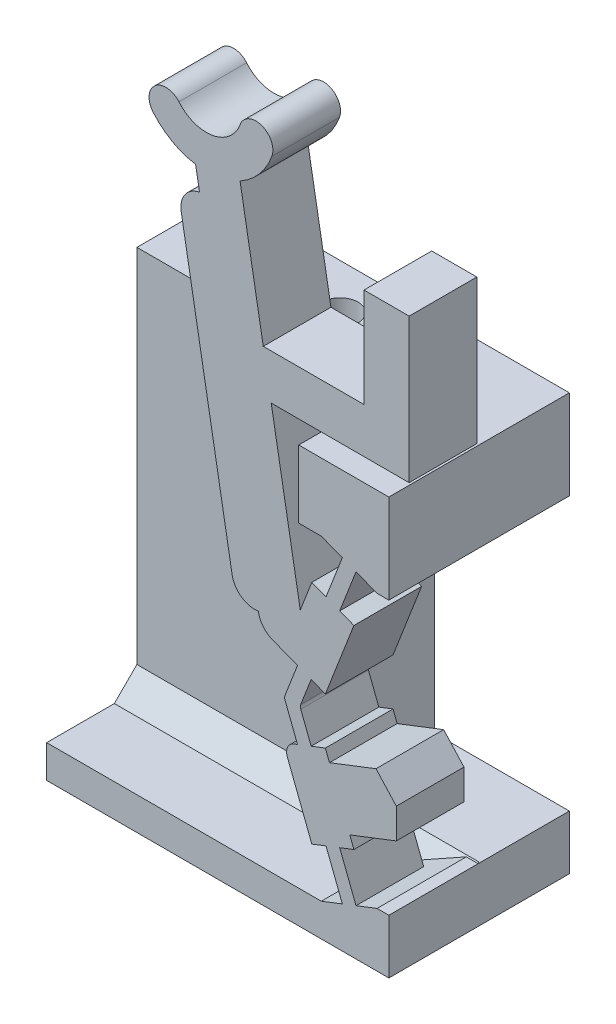
SolidWorks part; units mm, degrees
material "Nylon 6/12"
ref_plane "Front Plane" through (0, 0, 0) normal (0, 0, 1) x (1, 0, 0)
ref_plane "Top Plane" through (0, 0, 0) normal (0, 1, 0) x (1, 0, 0)
ref_plane "Right Plane" through (0, 0, 0) normal (1, 0, 0) x (0, 0, -1)
sketch "Sketch-SkeletonConfigUp" plane through (0, 0, 0) normal (0, 0, 1) x (1, 0, 0)
  line L0 (0, 0) -> (0, -50000) construction
  line L1 (-1.4217, 8.457) -> (-1.4217, 0) construction
  line L3 (0.7468, 14.0514) -> (-1.4217, 8.457) construction
  line L4 (-1.4217, 8.457) -> (0.7468, 2.8626) construction
  line L5 (0.7468, 14.0514) -> (2.1074, 19.3343) construction
  line L6 (-1.4217, 8.457) -> (-5.2203, 30) construction
  line L9 (0.7468, 14.0514) -> (0.7468, 2.8626) construction
  line L10 (0.7468, 2.8626) -> (0.7468, 0) construction
  line L11 (0, 0) -> (0.7468, 0) construction
  line L12 (0.7468, 0) -> (0, 0) construction
  dimension "D7" = 5.4552
  dimension "D10" = 6.745
  dimension "D3" = 2.1685
  dimension "D9" = 10
  dimension "D13" = 11.1888
  dimension "D14" = 30
  dimension "D5" = 10
  dimension "D2" = 21.8753
  dimension "D4" = 6
sketch "Sketch-SkeletonConfigDown" plane through (0, 0, 0) normal (0, 0, 1) x (1, 0, 0)
  line L0 (0, 0) -> (0, -50000) construction
  line L1 (0.7468, 14.0514) -> (0.7468, 2.8626) construction
  line L2 (5.9945, 14.5439) -> (0.7468, 14.0514) construction
  line L3 (0.7468, 14.0514) -> (2.9153, 8.457) construction
  line L4 (2.9153, 8.457) -> (0.7468, 2.8626) construction
  line L5 (0.7468, 14.0514) -> (-1.8086, 18.8711) construction
  line L6 (2.9153, 8.457) -> (-13.9344, 22.4075) construction
  line L7 (0.7468, 2.8626) -> (5.9945, 14.5439) construction
  line L8 (-387.6937, -861.8102) -> (5.9945, 14.5439) construction
  line L10 (-1.4217, 8.457) -> (0.7468, 2.8626) construction
  line L11 (0.7468, 14.0514) -> (-1.4217, 8.457) construction
  line L12 (-1.4217, 8.457) -> (-5.2203, 30) construction
  line L13 (0.7468, 14.0514) -> (2.1074, 19.3343) construction
  dimension "D10" = 6.745
  dimension "D4" = 5.2707
  dimension "D5" = 119.553
  dimension "D2" = 50.378
  dimension "D3" = 29.19
ref_plane "Plane-Cam Base" through (3.8672, 0, 0) normal (1, 0, 0) x (0, 0, -1)
ref_plane "Plane-Down-to-Up Derailleur Clearance" through (1.3672, 0, 0) normal (1, 0, 0) x (0, 0, -1)
ref_plane "Plane-Cam Cavity Roof" through (-0.1328, 0, 0) normal (1, 0, 0) x (0, 0, -1)
sketch "Sketch-SwitchBossUp" plane through (0, 0, 0) normal (0, 0, 1) x (1, 0, 0)
  line L8 (-5.6979, 26.9497) -> (-5.5242, 25.9649)
  line L9 (-1.4217, 8.457) -> (-5.2203, 30) construction
  line L15 (-1.1826, 6.941) -> (-0.5766, 7.1759) construction
  line L16 (-1.4217, 8.457) -> (0.7468, 2.8626) construction
  line L19 (0.0824, 13.2365) -> (0.6884, 13.0016) construction
  line L22 (0.8052, 15.1013) -> (1.4113, 14.8664) construction
  line L23 (-1.1826, 9.9731) -> (-1.812, 10.2171)
  line L32 (1.0498, 2.9801) -> (0.4438, 2.7452) construction
  line L40 (-1.7703, 8.457) -> (-1.0732, 8.457) construction
  line L66 (-5.2203, 27.8193) -> (-5.2203, 50027.8193) construction
  line L74 (-4.078, 12.0039) -> (-6.3354, 24.8064)
  line L81 (2.3437, 2.4091) -> (2.8672, 2.4091)
  line L82 (-5.6111, 26.4573) -> (-3.6415, 26.8046) construction
  line L88 (-0.1116, 18.4627) -> (2.8672, 18.4627)
  line L92 (0.6853, 5.7881) -> (-1.1795, 5.0653) construction
  line L95 (-2.3469, 19.4627) -> (3.7672, 19.4627)
  line L96 (2.8672, 14.505) -> (2.8672, 18.4627)
  line L97 (3.7672, 19.4627) -> (3.7672, 25.8576)
  line L101 (-0.8796, 7.0584) -> (-1.4217, 8.457) construction
  line L103 (-5.2203, 30) -> (-3.0238, 29.2005) construction
  line L107 (-1.1826, 9.9731) -> (-0.5766, 9.7382) construction
  line L109 (-5.2203, 30) -> (-7.011, 28.4975) construction
  line L114 (0.0528, 7.4199) -> (-0.5766, 7.1759)
  line L117 (2.8672, 0) -> (-0.1272, 0)
  line L121 (0.7468, 0) -> (0, 0) construction
  line L122 (0.8052, 1.8128) -> (-0.1272, 1.4513)
  line L123 (1.4113, 2.0477) -> (2.3437, 2.4091)
  line L125 (2.8672, 2.4091) -> (2.8672, 0)
  line L127 (-0.5766, 9.7382) -> (0.0528, 9.4942)
  line L133 (0.4438, 14.1689) -> (1.0498, 13.934) construction
  line L134 (0.0528, 9.4942) -> (1.3178, 12.7576)
  line L135 (0.6884, 13.0016) -> (1.3178, 12.7576)
  line L142 (-0.1272, 1.4513) -> (-0.1272, 0)
  line L151 (0.0824, 13.2365) -> (-0.547, 13.4805)
  line L152 (0.8052, 15.1013) -> (0.0824, 13.2365)
  line L153 (1.4113, 14.8664) -> (0.6884, 13.0016)
  line L169 (0.0824, 3.6776) -> (0.8052, 1.8128)
  line L170 (1.4113, 2.0477) -> (0.6884, 3.9125)
  line L177 (0.6884, 3.9125) -> (0.0824, 3.6776) construction
  line L184 (-0.547, 13.4805) -> (-1.0591, 12.1594)
  line L191 (-1.1826, 6.941) -> (-1.812, 6.697)
  line L197 (3.7672, 25.8576) -> (1.7672, 25.8576)
  line L205 (1.7672, 25.8576) -> (1.7672, 21.4627)
  line L207 (12.0045, 16.6962) -> (12.0045, 16.6883) construction
  line L218 (0.6884, 3.9125) -> (1.3178, 4.1564)
  line L225 (-1.0591, 12.1594) -> (-2.3469, 19.4627)
  line L235 (-5.5242, 25.9649) -> (-2.8161, 10.6063) construction
  line L236 (-1.812, 6.697) -> (-0.547, 3.4336)
  line L237 (-2.8161, 10.6063) -> (-2.9195, 11.1927)
  line L241 (-1.4217, 8.457) -> (-0.8796, 9.8556) construction
  line L242 (1.7672, 21.4627) -> (-2.6996, 21.4627)
  line L243 (-0.5766, 7.1759) -> (-1.0381, 8.3667)
  line L244 (-1.0381, 8.5474) -> (-0.5766, 9.7382)
  line L245 (-1.1826, 6.941) -> (-1.7353, 8.3667)
  line L246 (-1.7353, 8.5474) -> (-1.1826, 9.9731)
  line L247 (0.0528, 7.4199) -> (0.2353, 6.9492)
  line L248 (0.8052, 1.8128) -> (1.4113, 2.0477) construction
  line L249 (0.0824, 3.6776) -> (-0.547, 3.4336)
  line L250 (-1.812, 10.2171) -> (-0.547, 13.4805) construction
  line L251 (0.7468, 14.0514) -> (-1.4217, 8.457) construction
  line L252 (-1.2699, 11.6157) -> (0.5949, 10.8928) construction
  line L253 (-2.3469, 19.4627) -> (-2.6996, 21.4627) construction
  line L254 (-1.812, 10.2171) -> (-2.8161, 10.6063)
  line L255 (0.8052, 15.1013) -> (-0.1272, 15.4627)
  line L256 (1.4113, 14.8664) -> (2.3437, 14.505)
  line L257 (2.3437, 14.505) -> (2.8672, 14.505)
  line L258 (-2.6996, 21.4627) -> (-3.7283, 27.297)
  line L259 (3.8672, -23.7286) -> (3.8672, 23.7286) construction
  line L260 (0.2353, 6.9492) -> (2.2973, 7.7484)
  line L261 (3.1975, 6.7619) -> (3.1975, 5.4265)
  line L262 (3.1975, 5.4265) -> (1.1353, 4.6271)
  line L263 (0.6853, 5.7881) -> (3.1975, 6.7619) construction
  line L264 (1.1353, 4.6271) -> (0.6853, 5.7881) construction
  line L265 (1.1353, 4.6271) -> (1.3178, 4.1564)
  line L266 (0.6853, 5.7881) -> (0.2353, 6.9492) construction
  line L267 (0.2353, 6.9492) -> (0.6853, 5.7881) construction
  line L268 (0.6853, 5.7881) -> (1.1353, 4.6271) construction
  line L269 (0.2353, 6.9492) -> (0.6853, 5.7881) construction
  line L270 (0.6853, 5.7881) -> (1.1353, 4.6271) construction
  line L271 (3.1975, 6.7619) -> (2.2973, 7.7484)
  line L272 (1.8311, 5.6598) -> (3.8672, 4.8706) construction
  line L273 (2.9153, 8.457) -> (0.7468, 2.8626) construction
  line L274 (-0.2471, 5.4267) -> (2.2973, 7.7484) construction
  line L275 (-0.2471, 5.4267) -> (3.8672, 5.4267) construction
  line L276 (-0.1272, 15.4627) -> (-1.1272, 15.4627)
  line L277 (-1.1272, 15.4627) -> (-1.1272, 18.4627)
  line L278 (-1.1272, 18.4627) -> (-0.1116, 18.4627)
  arc A0 (-3.7283, 27.297) -> (-2.319, 28.944) centre (-5.2203, 30) ccw
  arc A1 (-5.6979, 26.9497) -> (-7.5855, 28.0154) centre (-5.2203, 30) cw
  arc A2 (-7.5855, 28.0154) -> (-6.4364, 28.9796) centre (-7.011, 28.4975) cw
  arc A3 (-2.319, 28.944) -> (-3.7286, 29.457) centre (-3.0238, 29.2005) ccw
  arc A4 (-6.4364, 28.9796) -> (-3.7286, 29.457) centre (-5.2203, 30) ccw
  arc A19 (-6.3354, 24.8064) -> (-5.5242, 25.9649) centre (-5.3506, 24.98) cw
  circle A28 centre (-5.2203, 30) radius 2.3375 construction
  arc A30 (-4.078, 12.0039) -> (-2.9195, 11.1927) centre (-3.0932, 12.1775) ccw
  arc A31 (-1.0381, 8.3667) -> (-1.0381, 8.5474) centre (-0.805, 8.457) cw
  arc A32 (-1.7353, 8.3667) -> (-1.7353, 8.5474) centre (-1.5022, 8.457) cw
  point P5 (-4.6263, 26.6309)
  point P6 (-0.2471, 5.4267)
  point P45 (-0.3375, 11.2542)
  point P66 (4.5811, 6.2164)
  point P165 (0.7468, 14.0514)
  dimension "D23" = 1.5875
  dimension "D24" = 0.75
  dimension "D21" = 0.25
  dimension "D8" = 0.65
  dimension "D27" = 0.65
  dimension "D26" = 2
  dimension "D3" = 1.5
  dimension "D5" = 1.5
  dimension "D16" = 2
  dimension "D28" = 2
  dimension "D29" = 2
  dimension "D30" = 1
  dimension "D31" = 15
  dimension "D4" = 1.4169
  dimension "D6" = 0.65
  dimension "D7" = 2
  dimension "D11" = 1
  dimension "D10" = 1
  dimension "D9" = 0
  dimension "D12" = 60
  dimension "D13" = 60
  dimension "D14" = 2
  dimension "D15" = 1
  dimension "D17" = 2
  dimension "D19" = 0.1
  dimension "D22" = 42.38
  dimension "D18" = 3
  dimension "D25" = 1
  dimension "D32" = 1
  dimension "D20" = 1
extrude "Boss-Switch Body" add sketch "Sketch-SwitchBossUp" along normal blind 3
sketch "Sketch1" plane through (0, 0, 0) normal (0, 0, -1) x (-1, 0, 0)
  line L0 (-2.8672, 2.4091) -> (0.1272, 2.4091)
  line L1 (-2.8672, 0) -> (0.1272, 0)
  line L2 (-2.8672, 0) -> (-2.8672, 2.4091)
  line L4 (0.1272, 0) -> (0.1272, 2.4091)
  line L5 (1.1272, 14.505) -> (-2.8672, 14.505)
  line L10 (-2.8672, 14.505) -> (-2.8672, 18.4627)
  line L12 (-2.8672, 18.4627) -> (1.1272, 18.4627)
  line L14 (1.1272, 18.4627) -> (1.1272, 14.505)
  line L20 (-2.3437, 2.4091) -> (-2.8672, 2.4091) construction
  line L22 (-2.8672, 2.4091) -> (-2.3437, 2.4091) construction
  line L31 (0.1272, 0) -> (-2.8672, 0) construction
  line L32 (0.1272, 1.4513) -> (0.1272, 0) construction
  point P8 (1.1272, 18.4627)
  point P9 (-2.8672, 14.505)
  point P10 (-2.8672, 15.2567)
  point P11 (-2.6275, 2.4091)
  point P16 (-2.8672, 2.4091)
  point P18 (-2.8672, 14.505)
  point P19 (0, 0)
  point P23 (-2.8672, 18.4627)
extrude "Boss-Flange Width" add sketch "Sketch1" along normal blind 5
ref_plane "Plane-Sta2Sit Groove" through (-5.2203, 0, 0) normal (1, 0, 0) x (0, 0, -1)
ref_plane "Plane-Cam Outer Surface" through (-17.3003, 0, 0) normal (1, 0, 0) x (0, 0, -1)
ref_plane "Plane-FlangeTop" through (-12.3003, 0, 0) normal (1, 0, 0) x (0, 0, -1)
sketch "Sketch2" plane through (-12.3003, 0, 0) normal (1, 0, 0) x (0, 0, -1)
  line L0 (5, 18.4627) -> (-3, 18.4627) construction
  line L1 (5, 14.505) -> (1, 14.505)
  line L2 (5, 14.505) -> (5, 18.4627)
  line L3 (5, 18.4627) -> (1, 18.4627)
  line L4 (1, 14.505) -> (1, 18.4627)
  line L5 (5, 14.505) -> (-3, 14.505) construction
  line L11 (5, 1.4513) -> (-3, 1.4513)
  line L12 (5, 1.4513) -> (5, 0)
  line L13 (5, 0) -> (-3, 0)
  line L14 (-3, 1.4513) -> (-3, 0)
  line L15 (0, 8.457) -> (0, 30) construction
  line L16 (-3, 1.4513) -> (-3, 0) construction
  line L17 (5, 2.4091) -> (5, 0) construction
  line L19 (-3, 1.4513) -> (0, 1.4513) construction
  dimension "D1" = 1
extrude "Boss-Flange Height" add sketch "Sketch2" along normal up to surface (12.1731 mm away) up to face at (-0.1272, 1.2868, -0.6667)
sketch "Sketch17" plane through (0, 1.4513, 0) normal (0, -1, 0) x (1, 0, 0)
  line L0 (2.8672, -5) -> (-12.3003, -5)
  line L1 (2.8672, -5) -> (-12.3003, -5) construction
  line L2 (-12.3003, -5) -> (-12.3003, -1)
  line L3 (-12.3003, -1) -> (2.8672, -1)
  line L4 (2.8672, -1) -> (2.8672, -5)
  line L5 (-12.3003, -1) -> (-12.3003, -5) construction
  line L7 (-1.1272, -1) -> (-12.3003, -1) construction
extrude "Boss-Flange Support" add sketch "Sketch17" against normal up to surface (13.0536 mm away) up to face at (-1.4588, 14.505, -0.6)
sketch "Sketch27" plane through (0, 0, 0) normal (0, 0, 1) x (1, 0, 0)
  line L1 (-0.1272, 15.4627) -> (2.3437, 14.505)
  line L2 (2.3437, 14.505) -> (-1.1272, 14.505)
  line L3 (-1.1272, 14.505) -> (-1.1272, 15.4627)
  line L4 (-1.1272, 15.4627) -> (-0.1272, 15.4627)
  line L6 (-1.1272, 14.505) -> (2.8672, 14.505) construction
  line L7 (2.3437, 14.505) -> (1.2712, 14.505) construction
  line L8 (2.3437, 2.4091) -> (-0.1272, 2.4091)
  line L9 (-0.1272, 2.4091) -> (-0.1272, 1.4513)
  line L10 (-0.1272, 1.4513) -> (2.3437, 2.4091)
extrude "Cut-Wall Gap" cut sketch "Sketch27" against normal up to surface (1 mm away) up to face at (-2.6719, 9.207, -1)
ref_plane "Plane-Tap Depth" through (0, 13.4627, 0) normal (0, 1, 0) x (1, 0, 0)
sketch "Sketch-HolePositions" plane through (0, 0, 0) normal (0, -1, 0) x (1, 0, 0)
  line L0 (-12.3003, -3) -> (2.8672, -3) construction
  line L1 (2.8672, -5) -> (-12.3003, -5) construction
  line L2 (2.8672, -5) -> (2.8672, 3) construction
  line L4 (-12.3003, -22.2167) -> (-12.3003, 22.2167) construction
  point P6 (-9.3003, -3)
  point P7 (-5.3003, -3)
  dimension "D1" = 3
  dimension "D2" = 4
  dimension "D3" = 2
sketch "Sketch6" plane through (0, 0, 0) normal (0, -1, 0) x (-1, 0, 0)
  point P0 (9.3003, 3)
  point P3 (5.3003, 3)
hole_wizard "Tap Drill for M2x0.4 Tap1" positions "Sketch6" profile "Sketch5" hole size "M2x0.4" standard "ANSI Metric" end condition through all
sketch "Sketch5" plane through (-9.3003, 0, -3) normal (1, 0, 0) x (0, 0, -1)
  line L0 (0, 0) -> (0, 29.9505)
  line L1 (0, 29.9505) -> (0.8, 29.9505)
  line L2 (0.8, 29.9505) -> (0.8, 0)
  line L5 (0.8, 0) -> (0, 0)
  line L11 (0, -6.35) -> (0, 107.95) construction
  dimension "Thru Hole Dia." = 1.6
  dimension "Thru Hole Depth" = 29.9505
sketch "Sketch9" plane through (0, 0, 0) normal (0, -1, 0) x (1, 0, 0)
  point P0 (-9.3003, -3)
  point P3 (-5.3003, -3)
hole_wizard "M2 Clearance Hole2" positions "Sketch9" profile "Sketch8" hole size "M2" standard "ANSI Metric"
sketch "Sketch8" plane through (-9.3003, 0, -3) normal (1, 0, 0) x (0, 0, -1)
  line L0 (0, 0) -> (0, 14.1838)
  line L1 (0, 14.1838) -> (1.2, 13.4627)
  line L2 (1.2, 13.4627) -> (1.2, 0)
  line L5 (1.2, 0) -> (0, 0)
  line L10 (0, 14.1838) -> (-1.2, 13.4627) construction
  line L11 (0, -6.35) -> (0, 107.95) construction
  dimension "Hole Dia." = 2.4
  dimension "Hole Depth" = 13.4627
  dimension "Drill Angle" = 118
sketch "Sketch-Measurements for Derailleur Ramps" [suppressed] plane through (0, 0, 0) normal (0, 0, 1) x (1, 0, 0)
  line L0 (2.8784, 16.9852) -> (4.2265, 19.8331)
  line L1 (3.5524, 18.4092) -> (3.0492, 18.6474)
  line L2 (1.9779, 11.0613) -> (4.4465, 28.5428) construction
  line L3 (3.0492, 18.6474) -> (-4.0642, 13.8428)
  line L4 (7.1843, 11.0614) -> (-9.9544, 15.2993) construction
  line L5 (3.0492, 18.6474) -> (2.1536, 12.3053)
  line L6 (2.1536, 12.3053) -> (-4.0642, 13.8428)
  line L7 (-0.5075, 16.2451) -> (-0.5075, 18.6474)
  line L8 (-0.5075, 18.6474) -> (3.0492, 18.6474)
  line L9 (7.1843, 11.0614) -> (1.9779, 11.0613)
  line L10 (5.8827, 8.6389) -> (3.2795, 8.6389)
  line L12 (7.1843, 11.0614) -> (4.5811, 6.2164) construction
  line L13 (4.5811, 8.6389) -> (4.5811, 8.7912)
  line L14 (4.5811, 6.2164) -> (5.8827, 8.6389)
  line L15 (1.9779, 11.0613) -> (4.5811, 6.2164) construction
  line L16 (3.2795, 8.6389) -> (4.5811, 6.2164)
  line L17 (5.8827, 8.6389) -> (5.8827, 8.7912)
  dimension "D1" = 3.5567
  dimension "D2" = 1.3016
sketch "Sketch12" [suppressed] plane through (0, 23.1883, 0) normal (0, 1, 0) x (1, 0, 0)
  line L0 (10.0045, 0) -> (12.0045, -3)
  line L1 (12.0045, -3) -> (12.0045, 0)
  line L2 (12.0045, 0) -> (10.0045, 0)
extrude "Cut-Up-to-Down Cantilever Slope" [suppressed] cut sketch "Sketch12" against normal up to next
ref_plane "Plane1" [suppressed] through (0, 6.9404, 0) normal (0, 1, 0) x (1, 0, 0)
sketch "Sketch-Derailleur Location" [suppressed] plane through (0, 6.9404, 0) normal (0, 1, 0) x (1, 0, 0)
  line L0 (12.9465, 0) -> (12.9465, -3)
  line L1 (4.2399, -3) -> (3.2603, -3) construction
  line L2 (-119237.4187, 0) -> (9.8143, 0) construction
  point P0 (12.9465, 0)
  point P8 (12.9465, -1.5)
ref_plane "Plane-Cantilever Cut" [suppressed] through (7.0848, 8.5204, -1.9058) normal (-0.6301, -0.7578, 0.1695) x (-0.7765, 0.6151, -0.1368)
sketch "Sketch14" [suppressed] plane through (7.0848, 8.5204, -1.9058) normal (-0.6301, -0.7578, 0.1695) x (-0.7765, 0.6151, -0.1368)
  line L0 (2.3023, -1.6911) -> (-0.3551, -1.6911)
  line L2 (2.3023, -4.3362) -> (2.3023, -1.6911)
  line L3 (-0.3551, -1.6911) -> (-0.3551, -4.4608)
  line L5 (-0.3551, -4.4608) -> (1.0087, -5.0843)
  line L6 (1.0087, -5.0843) -> (2.3023, -4.3362)
extrude "Cut-Down-to-Up Cantilever Slope" [suppressed] cut sketch "Sketch14" against normal up to next
ref_plane "Plane-Symmetry Plane" through (0, 0, 1.5) normal (0, 0, 1) x (1, 0, 0)
sketch "Sketch-Cable Center Point" plane through (0, 0, 1.5) normal (0, 0, 1) x (1, 0, 0)
  line L0 (-5.2203, 30) -> (-5.0825, 29.2183)
  line L1 (-1.4217, 8.457) -> (-5.2203, 30) construction
  point P0 (-5.2203, 30)
  dimension "D1" = 0.7937
sketch "Sketch28" plane through (0, 0, -1) normal (0, 0, 1) x (1, 0, 0)
  line L0 (2.8672, 14.505) -> (2.8672, 2.4091)
  line L1 (2.3437, 2.4091) -> (2.8672, 2.4091) construction
  line L2 (2.8672, 14.505) -> (-3.1003, 14.505)
  line L3 (-3.1003, 14.505) -> (-3.1003, 2.4091)
  line L4 (-3.1003, 2.4091) -> (2.8672, 2.4091)
  line L6 (-6.5003, 13.4627) -> (-4.1003, 13.4627) construction
  line L7 (-6.5003, 13.4627) -> (-4.1003, 13.4627) construction
  dimension "D1" = 1
chamfer "Chamfer-Flange Support" [suppressed] distance 1.5 angle 45
chamfer "Chamfer-Flange Support 3" distance 1 angle 45 1 edges at (-6.2138, 1.4513, -1)
fillet "Fillet1" radius 1 1 edges at (-2.8161, 10.6063, 1.5)
fillet "Fillet2" radius 0.5 1 edges at (-1.812, 6.697, 1.5)
extrude "Cut-Print Support Clearance" cut sketch "Sketch28" against normal through all
equation "\"axle-diameter\"=2"
equation "\"switch-thickness\"=12"
equation "\"base-width\"=4.0"
equation "\"axle-bushing-radius\"=3"
equation "\"clearance\"= 0.25"
equation "\"arm-width\"=1.5"
equation "\"min-diameter\"=70"
equation "\"alpha\"=143.6120"
equation "\"gamma\"=119.5526"
equation "\"delta\"=145.9637"
equation "\"epsilon\"=6.7452"
equation "\"l_AB\"=8.8212"
equation "\"l_AC\"=4.4914"
equation "\"l_BD\"=5.2707"
equation "\"l_CD\"=3.8848"
equation "\"l_CE\"=10.9181"
equation "\"l_DF\"=5.4552"
equation "\"l_OA\"=7.7221"
equation "\"D7@Sketch-SkeletonConfigUp\" = \"l_DF\""
equation "\"D_groove\"=3.175"
equation "\"D5@Sketch-SkeletonConfigDown\" = \"gamma\""
equation "\"D4@Sketch-SkeletonConfigDown\" = \"l_BD\""
equation "\"hinge_length\"=1.5"
equation "\"hinge_depth\"=0.25"
equation "\"D10@Sketch-SkeletonConfigUp\"=\"epsilon\""
equation "\"D10@Sketch-SkeletonConfigDown\"=\"epsilon\""
equation "\"EE_dx\"=8.9056"
equation "\"EE_dy\"=8.1898"
equation "\"r_groove\"=\"D_groove\"/2"
equation "\"t_wall\"=25.4/16"
equation "\"width_lower\"=\"D_groove\"+\"t_wall\""
equation "\"cable_to_bottom\"=30.6257"
equation "\"switch_EE-up_base_dy\"=24"
equation "\"switch_EE-down_base_dy\"=16"
equation "\"D_axle\"=25.4/8"
equation "\"D_up_to_down\"=16"
equation "\"D_down_to_up\"=25"
equation "\"t_cam_base\"=7.5"
equation "\"D23@Sketch-SwitchBossUp\"=\"D_groove\"/2"
equation "\"D1@Sketch-Cable Center Point\"=\"D_groove\"/4"
